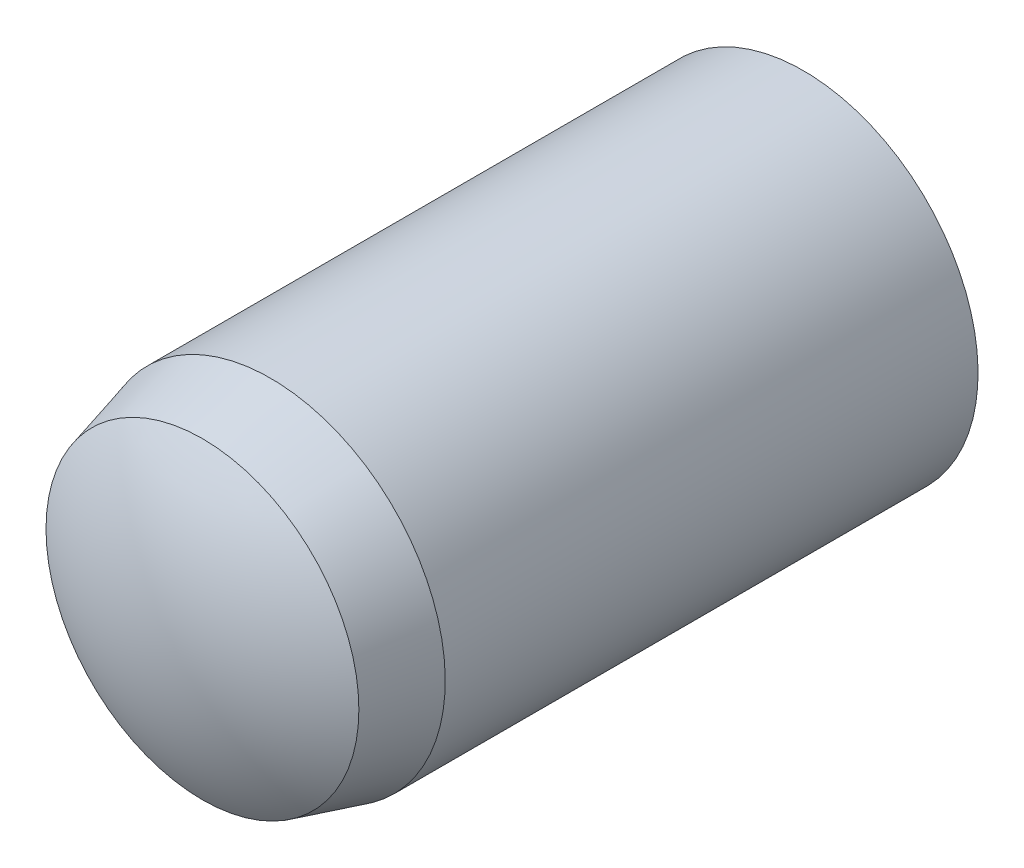
SolidWorks part; units mm, degrees
ref_plane "Front Plane" through (0, 0, 0) normal (0, 0, 1) x (1, 0, 0)
ref_plane "Top Plane" through (0, 0, 0) normal (0, 1, 0) x (1, 0, 0)
ref_plane "Right Plane" through (0, 0, 0) normal (1, 0, 0) x (0, 0, -1)
sketch "Sketch1" plane through (0, 0, 0) normal (0, 0, 1) x (1, 0, 0)
  circle A0 centre (0, 0) radius 5
  point P3 (0, 5)
  dimension "Diameter" = 10
sketch "Sketch2" plane through (0, 0, 0) normal (1, 0, 0) x (0, 0, -1)
  line L0 (-10, 0) -> (10, 0) construction
  line L1 (-10, 0) -> (-10, 5) construction
  line L2 (-10, 5) -> (10, 5)
  line L3 (10, 5) -> (10, 0) construction
  line L4 (-8.7, 4.4775) -> (-6.75, 5)
  arc A0 (-10, 0) -> (-8.7, 4.4775) centre (-1.6392, 0) cw
  arc A1 (10, 0) -> (8.5, 5) centre (0.9167, 0) ccw
  point P2 (0, 0)
  dimension "Length" = 20
  dimension "D1" = 15
  dimension "D2" = 1.5
  dimension "D3" = 3.25
  dimension "D4" = 1.95
sketch "Sketch3" plane through (0, 0, 0) normal (1, 0, 0) x (0, 0, -1)
  line L0 (-10, 0) -> (10, 0) construction
  line L1 (-8.7, 4.4775) -> (-6.75, 5) construction
  line L2 (-10, 0) -> (10, 0)
  line L3 (-8.7, 4.4775) -> (-6.75, 5)
  line L4 (-6.75, 5) -> (8.5, 5)
  arc A0 (10, 0) -> (8.5, 5) centre (0.9167, 0) ccw construction
  arc A1 (-8.7, 4.4775) -> (-10, 0) centre (-1.6392, 0) ccw construction
  arc A2 (10, 0) -> (8.5, 5) centre (0.9167, 0) ccw
  arc A3 (-8.7, 4.4775) -> (-10, 0) centre (-1.6392, 0) ccw
revolve "Revolve1" add sketch "Sketch3" angle 360 about L2
equation "\"D2@Sketch2\" = \"Diameter@Sketch1\" * .15"
equation "\"D3@Sketch2\" = \"Diameter@Sketch1\" * .325"
equation "\"D4@Sketch2\" = \"D3@Sketch2\" * .6"
